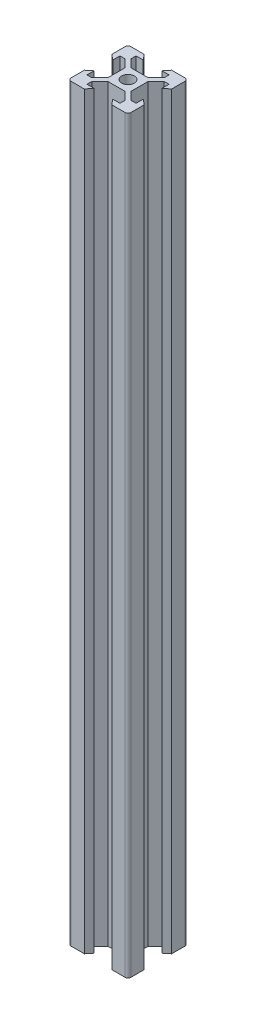
SolidWorks part; units mm, degrees
ref_plane "Front Plane" through (0, 0, 0) normal (0, 0, 1) x (1, 0, 0)
ref_plane "Top Plane" through (0, 0, 0) normal (0, 1, 0) x (1, 0, 0)
ref_plane "Right Plane" through (0, 0, 0) normal (1, 0, 0) x (0, 0, -1)
sketch "Sketch1" plane through (0, 0, 0) normal (0, 1, 0) x (1, 0, 0)
  line L0 (-3.125, 8.2) -> (-4.58, 10)
  line L1 (-9, 10) -> (9, 10)
  line L2 (-10, 9) -> (-10, -9)
  line L3 (-9, -10) -> (9, -10)
  line L4 (10, 9) -> (10, -9)
  line L5 (-10, 10) -> (10, -10) construction
  line L6 (-10, -10) -> (10, 10) construction
  line L7 (-10, 0) -> (0, 0) construction
  line L8 (0, 10) -> (0, 0) construction
  line L9 (-8.2, 3.125) -> (-10, 4.58)
  line L10 (-8.2, 3.125) -> (-8.2, 5.5)
  line L11 (-3.125, 8.2) -> (-5.5, 8.2)
  line L12 (-5.5, 8.2) -> (-5.5, 6.56)
  line L13 (-2.84, 3.9) -> (2.84, 3.9)
  line L14 (-5.5, 6.56) -> (-2.84, 3.9)
  line L15 (-8.2, 5.5) -> (-6.56, 5.5)
  line L16 (-6.56, 5.5) -> (-3.9, 2.84)
  line L17 (-3.9, 2.84) -> (-3.9, -2.84)
  line L18 (3.9, 2.84) -> (3.9, -2.84)
  line L19 (6.56, 5.5) -> (3.9, 2.84)
  line L20 (8.2, 5.5) -> (6.56, 5.5)
  line L21 (8.2, 3.125) -> (8.2, 5.5)
  line L22 (8.2, 3.125) -> (10, 4.58)
  line L23 (3.125, 8.2) -> (4.58, 10)
  line L24 (3.125, 8.2) -> (5.5, 8.2)
  line L25 (5.5, 8.2) -> (5.5, 6.56)
  line L26 (5.5, 6.56) -> (2.84, 3.9)
  line L27 (-8.2, -3.125) -> (-10, -4.58)
  line L28 (-8.2, -3.125) -> (-8.2, -5.5)
  line L29 (-8.2, -5.5) -> (-6.56, -5.5)
  line L30 (-6.56, -5.5) -> (-3.9, -2.84)
  line L31 (8.2, -3.125) -> (10, -4.58)
  line L32 (8.2, -3.125) -> (8.2, -5.5)
  line L33 (8.2, -5.5) -> (6.56, -5.5)
  line L34 (6.56, -5.5) -> (3.9, -2.84)
  line L35 (5.5, -6.56) -> (2.84, -3.9)
  line L36 (5.5, -8.2) -> (5.5, -6.56)
  line L37 (3.125, -8.2) -> (5.5, -8.2)
  line L38 (3.125, -8.2) -> (4.58, -10)
  line L39 (-5.5, -6.56) -> (-2.84, -3.9)
  line L40 (-2.84, -3.9) -> (2.84, -3.9)
  line L41 (-5.5, -8.2) -> (-5.5, -6.56)
  line L42 (-3.125, -8.2) -> (-5.5, -8.2)
  line L43 (-3.125, -8.2) -> (-4.58, -10)
  circle A0 centre (0, 0) radius 2.1
  arc A1 (-10, -9) -> (-9, -10) centre (-9, -9) ccw
  arc A2 (9, -10) -> (10, -9) centre (9, -9) ccw
  arc A3 (9, 10) -> (10, 9) centre (9, 9) cw
  arc A4 (-9, 10) -> (-10, 9) centre (-9, 9) ccw
  point P0 (0, 0)
  point P35 (0, 3.9)
  point P40 (-3.9, 0)
  point P41 (3.9, 0)
  dimension "D3" = 4.2
  dimension "D2" = 1
  dimension "D1" = 20
  dimension "D4" = 6.1
  dimension "D5" = 6.25
  dimension "D6" = 11
  dimension "D7" = 5.68
  dimension "D8" = 9.16
  dimension "D9" = 1.8
extrude "Boss-Extrude1" add sketch "Sketch1" along normal blind 250 contours L43 L42 L41 L39 L40 L35 L36 L37 L38 L3 L4 L31 L32 L33 L34 L18 L19 L20 L21 L22 L1 L23 L24 L25 L26 L13 L14 L12 L11 L0 L2 L9 L10 L15 L16 L17 L30 L29 L28 L27 A0
